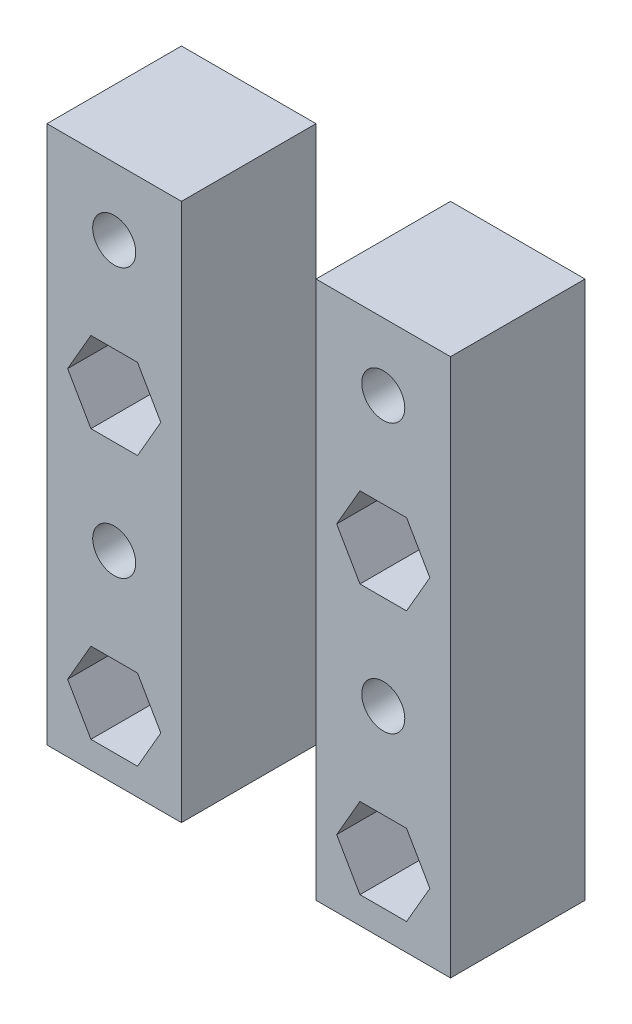
SolidWorks part; units mm, degrees
ref_plane "Front Plane" through (0, 0, 0) normal (0, 0, 1) x (1, 0, 0)
ref_plane "Top Plane" through (0, 0, 0) normal (0, 1, 0) x (1, 0, 0)
ref_plane "Right Plane" through (0, 0, 0) normal (1, 0, 0) x (0, 0, -1)
sketch "Sketch1" plane through (0, 0, 0) normal (0, 0, 1) x (1, 0, 0)
  line L0 (10, 0) -> (10, -10)
  line L1 (0, 0) -> (30, 0)
  line L2 (0, 0) -> (0, 30)
  line L3 (0, 30) -> (30, 30)
  line L4 (30, 0) -> (30, 30)
  line L5 (30, 30) -> (20, 30)
  line L6 (30, 30) -> (30, 0)
  line L7 (30, 0) -> (20, 0)
  line L8 (20, 30) -> (20, 0)
  line L9 (0, 30) -> (10, 30)
  line L10 (0, 30) -> (0, 0)
  line L11 (0, 0) -> (10, 0)
  line L12 (10, 30) -> (10, 0)
  line L13 (0, 0) -> (30, 0)
  line L14 (0, 0) -> (0, -10)
  line L15 (0, -10) -> (30, -10)
  line L16 (30, 0) -> (30, -10)
  line L17 (20, 0) -> (20, -10)
  circle A0 centre (5, 5) radius 1.6
  circle A1 centre (5, 25) radius 1.6
  circle A2 centre (25, 25) radius 1.6
  circle A3 centre (25, 5) radius 1.6
  circle A4 centre (5, -5) radius 1.6
  circle A5 centre (25, -5) radius 1.6
  circle A6 centre (25, 15) radius 1.6
  circle A7 centre (5, 15) radius 1.6
  point P9 (10, 15)
  dimension "D5" = 20
  dimension "D6" = 20
  dimension "D7" = 20
  dimension "D8" = 20
  dimension "D9" = 5
  dimension "D10" = 5
  dimension "D11" = 5
  dimension "D12" = 5
  dimension "D13" = 3.2
  dimension "D14" = 3.2
  dimension "D15" = 3.2
  dimension "D16" = 3.2
  dimension "D18" = 3.2
  dimension "D19" = 3.2
  dimension "D20" = 3.2
  dimension "D21" = 3.2
  dimension "D22" = 5
  dimension "D23" = 5
  dimension "D24" = 5
  dimension "D25" = 5
  dimension "D26" = 10
  dimension "D27" = 5
  dimension "D28" = 10
  dimension "D29" = 5
  dimension "D1" = 10
  dimension "D2" = 10
  dimension "D3" = 30
  dimension "D4" = 30
  dimension "D17" = 10
extrude "Boss-Extrude1" add sketch "Sketch1" along normal blind 10 contours L12 L3 L2 L1 A7 A1 A0 | L14 L15 L0 L1 A4 | L3 L8 L1 L4 A6 A3 A2 | L1 L17 L15 L16 A5
sketch "Sketch4" plane through (0, 0, 10) normal (0, 0, 1) x (1, 0, 0)
  line L0 (20, -10) -> (30, -10) construction
  line L1 (6.7321, -2) -> (3.2679, -2)
  line L2 (3.2679, -2) -> (1.5359, -5)
  line L3 (1.5359, -5) -> (3.2679, -8)
  line L4 (3.2679, -8) -> (6.7321, -8)
  line L5 (6.7321, -8) -> (8.4641, -5)
  line L6 (8.4641, -5) -> (6.7321, -2)
  line L7 (8.4641, 15) -> (6.7321, 18)
  line L8 (6.7321, 18) -> (3.2679, 18)
  line L9 (3.2679, 18) -> (1.5359, 15)
  line L10 (1.5359, 15) -> (3.2679, 12)
  line L11 (3.2679, 12) -> (6.7321, 12)
  line L12 (6.7321, 12) -> (8.4641, 15)
  line L13 (28.4641, 15) -> (26.7321, 18)
  line L14 (26.7321, 18) -> (23.2679, 18)
  line L15 (23.2679, 18) -> (21.5359, 15)
  line L16 (21.5359, 15) -> (23.2679, 12)
  line L17 (23.2679, 12) -> (26.7321, 12)
  line L18 (26.7321, 12) -> (28.4641, 15)
  line L19 (28.4641, -5) -> (26.7321, -2)
  line L20 (26.7321, -2) -> (23.2679, -2)
  line L21 (23.2679, -2) -> (21.5359, -5)
  line L22 (21.5359, -5) -> (23.2679, -8)
  line L23 (23.2679, -8) -> (26.7321, -8)
  line L24 (26.7321, -8) -> (28.4641, -5)
  circle A0 centre (5, -5) radius 3 construction
  circle A1 centre (5, 15) radius 3 construction
  circle A2 centre (25, 15) radius 3 construction
  circle A3 centre (25, -5) radius 3 construction
  point P28 (25, 18)
  circle M17 centre (25, 15) radius 1.6
  circle M24 centre (25, -5) radius 1.6
  dimension "D1" = 6
  dimension "D2" = 6
  dimension "D3" = 6
  dimension "D4" = 6
extrude "Cut-Extrude1" cut sketch "Sketch4" against normal blind 5 contours L5 L6 L1 L2 L3 L4 | L11 L12 L7 L8 L9 L10 | L17 L18 L13 L14 L15 L16 M17 | L23 L24 L19 L20 L21 L22 M24
